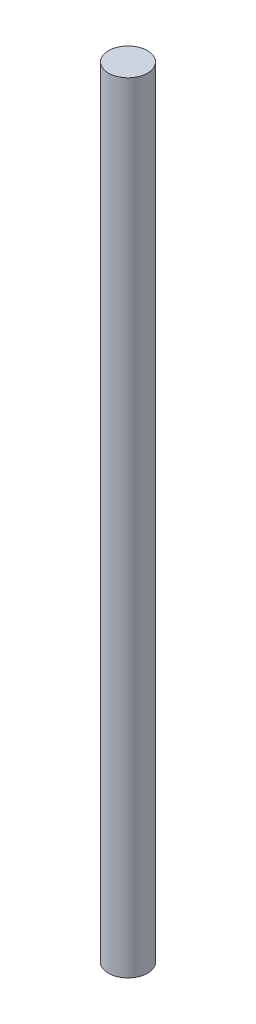
SolidWorks part; units mm, degrees
material "AISI 4340 Steel, normalized"
ref_plane "Front Plane" through (0, 0, 0) normal (0, 0, 1) x (1, 0, 0)
ref_plane "Top Plane" through (0, 0, 0) normal (0, 1, 0) x (1, 0, 0)
ref_plane "Right Plane" through (0, 0, 0) normal (1, 0, 0) x (0, 0, -1)
sketch "Sketch1" plane through (0, 0, 0) normal (0, 1, 0) x (1, 0, 0)
  circle A0 centre (0, 0) radius 0.25
  dimension "D1" = 0.5
extrude "Boss-Extrude1" add sketch "Sketch1" along normal mid plane 1.5
sketch "Sketch2" plane through (0, 0.75, 0) normal (0, 1, 0) x (1, 0, 0)
  circle A1 centre (0, 0) radius 0.25
  circle A2 centre (0, 0) radius 0.25
  dimension "D1" = 0
extrude "Boss-Extrude2" add sketch "Sketch2" along normal blind 4.25
sketch "Sketch3" plane through (0, -0.75, 0) normal (0, -1, 0) x (1, 0, 0)
  circle A1 centre (0, 0) radius 0.25
  circle A2 centre (0, 0) radius 0.25
  dimension "D1" = 0
extrude "Boss-Extrude3" add sketch "Sketch3" along normal blind 4.25
